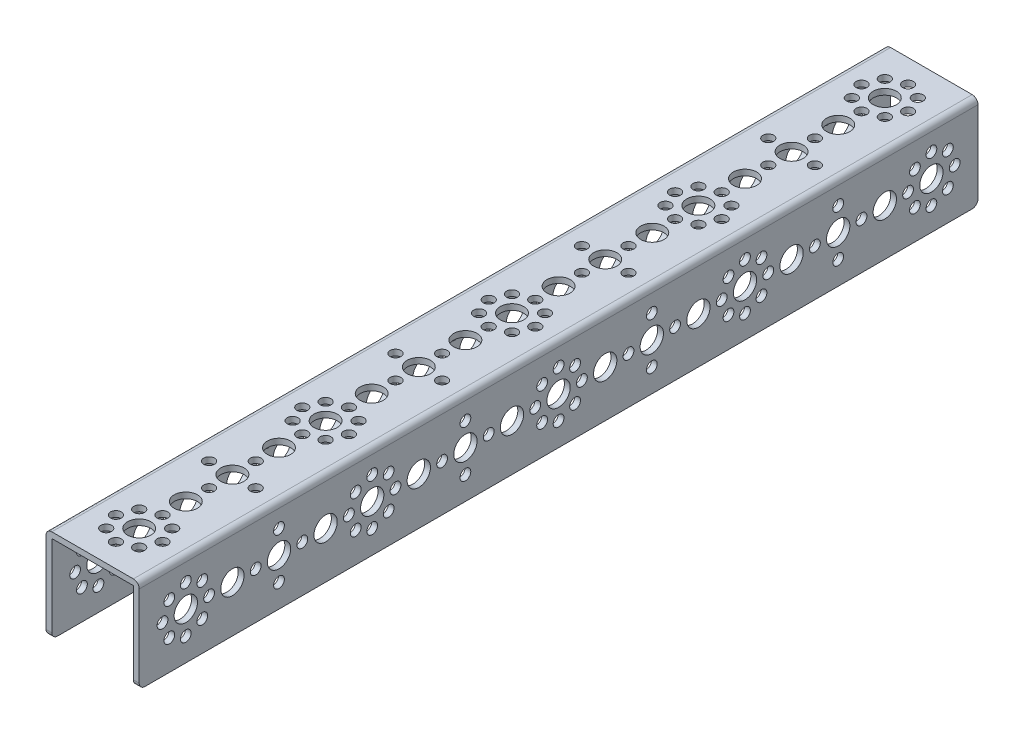
SolidWorks part; units mm, degrees
ref_plane "Front Plane" through (0, 0, 0) normal (0, 0, 1) x (1, 0, 0)
ref_plane "Top Plane" through (0, 0, 0) normal (0, 1, 0) x (1, 0, 0)
ref_plane "Right Plane" through (0, 0, 0) normal (1, 0, 0) x (0, 0, -1)
sketch "Sketch1" plane through (0, 0, 0) normal (0, 0, 1) x (1, 0, 0)
  line L0 (14, -16) -> (16, -16)
  line L1 (-16, 16) -> (16, 16)
  line L2 (-16, 16) -> (-16, -16)
  line L3 (-16, -16) -> (-14, -16)
  line L4 (16, 16) -> (16, -16)
  line L5 (-16, 16) -> (16, -16) construction
  line L6 (-16, -16) -> (16, 16) construction
  line L7 (-14, 14) -> (14, 14)
  line L8 (-14, 14) -> (-14, -16)
  line L10 (14, 14) -> (14, -16)
  point P0 (0, 0)
  dimension "D1" = 32
  dimension "D2" = 32
  dimension "D3" = 2
  dimension "D4" = 2
extrude "Boss-Extrude1" add sketch "Sketch1" against normal blind 288
sketch "Sketch2" plane through (0, 16, 0) normal (0, 1, 0) x (1, 0, 0)
  line L0 (0, 0) -> (0, 307.3895) construction
  line L1 (16, 0) -> (-16, 0) construction
  line L2 (-26.7249, 144) -> (42.2171, 144) construction
  circle B0 centre (0, 256) radius 4
  circle B1 centre (0, 224) radius 4
  circle B2 centre (0.1754, 192) radius 4
  circle B3 centre (0, 160) radius 4
  circle B4 centre (0, 240) radius 4
  circle B5 centre (0, 232) radius 1.85
  circle B6 centre (0, 248) radius 1.85
  circle B7 centre (-8, 240) radius 1.85
  circle B8 centre (8, 240) radius 1.85
  circle B9 centre (0, 264) radius 1.85
  circle B10 centre (-8, 272) radius 1.85
  circle B11 centre (0, 272) radius 4
  circle B12 centre (8, 272) radius 1.85
  circle B13 centre (5.66, 277.66) radius 1.85
  circle B14 centre (-5.66, 277.66) radius 1.85
  circle B15 centre (0, 280) radius 1.85
  circle B16 centre (5.66, 266.34) radius 1.85
  circle B17 centre (-5.66, 266.34) radius 1.85
  circle B18 centre (0, 176) radius 4
  circle B19 centre (0, 168) radius 1.85
  circle B20 centre (0, 184) radius 1.85
  circle B21 centre (-8, 176) radius 1.85
  circle B22 centre (8, 176) radius 1.85
  circle B23 centre (0, 200) radius 1.85
  circle B24 centre (-8, 208) radius 1.85
  circle B25 centre (0, 208) radius 4
  circle B26 centre (8, 208) radius 1.85
  circle B27 centre (5.66, 213.66) radius 1.85
  circle B28 centre (-5.66, 213.66) radius 1.85
  circle B29 centre (0, 216) radius 1.85
  circle B30 centre (5.66, 202.34) radius 1.85
  circle B31 centre (-5.66, 202.34) radius 1.85
  circle B32 centre (0, 32) radius 4
  circle B33 centre (0, 64) radius 4
  circle B34 centre (-0.1754, 96) radius 4
  circle B35 centre (0, 128) radius 4
  circle B36 centre (0, 48) radius 4
  circle B37 centre (0, 56) radius 1.85
  circle B38 centre (0, 40) radius 1.85
  circle B39 centre (8, 48) radius 1.85
  circle B40 centre (-8, 48) radius 1.85
  circle B41 centre (0, 24) radius 1.85
  circle B42 centre (8, 16) radius 1.85
  circle B43 centre (0, 16) radius 4
  circle B44 centre (-8, 16) radius 1.85
  circle B45 centre (-5.66, 10.34) radius 1.85
  circle B46 centre (5.66, 10.34) radius 1.85
  circle B47 centre (0, 8) radius 1.85
  circle B48 centre (-5.66, 21.66) radius 1.85
  circle B49 centre (5.66, 21.66) radius 1.85
  circle B50 centre (0, 112) radius 4
  circle B51 centre (0, 120) radius 1.85
  circle B52 centre (0, 104) radius 1.85
  circle B53 centre (8, 112) radius 1.85
  circle B54 centre (-8, 112) radius 1.85
  circle B55 centre (0, 88) radius 1.85
  circle B56 centre (8, 80) radius 1.85
  circle B57 centre (0, 80) radius 4
  circle B58 centre (-8, 80) radius 1.85
  circle B59 centre (-5.66, 74.34) radius 1.85
  circle B60 centre (5.66, 74.34) radius 1.85
  circle B61 centre (0, 72) radius 1.85
  circle B62 centre (-5.66, 85.66) radius 1.85
  circle B63 centre (5.66, 85.66) radius 1.85
  circle B64 centre (0, 136) radius 1.85
  circle B65 centre (-8, 144) radius 1.85
  circle B66 centre (0, 144) radius 4
  circle B67 centre (8, 144) radius 1.85
  circle B68 centre (5.66, 149.66) radius 1.85
  circle B69 centre (-5.66, 149.66) radius 1.85
  circle B70 centre (0, 152) radius 1.85
  circle B71 centre (5.66, 138.34) radius 1.85
  circle B72 centre (-5.66, 138.34) radius 1.85
sketch_block_instance "TETRIX 288 Pattern-3"
sketch_block "TETRIX 288 Pattern" parameters "D1"=16, "D2"=16, "D3"=16, "D4"=16, "D5"=16, "D6"=16, "D7"=16, "D8"=16, "D9"=16, "D10"=16, "D11"=16, "D12"=16, "D13"=16, "D14"=16, "D15"=16
extrude "Cut-Extrude1" cut sketch "Sketch2" against normal through all
sketch "Sketch3" plane through (16, 0, 0) normal (1, 0, 0) x (0, 0, -1)
  line L0 (-3.4954, 0) -> (176.3323, 0) construction
  line L1 (144, 24.5569) -> (144, -31.5997) construction
  circle B0 centre (32, 0) radius 4
  circle B1 centre (64, 0) radius 4
  circle B2 centre (96, 0.1754) radius 4
  circle B3 centre (128, 0) radius 4
  circle B4 centre (48, 0) radius 4
  circle B5 centre (56, 0) radius 1.85
  circle B6 centre (40, 0) radius 1.85
  circle B7 centre (48, -8) radius 1.85
  circle B8 centre (48, 8) radius 1.85
  circle B9 centre (24, 0) radius 1.85
  circle B10 centre (16, -8) radius 1.85
  circle B11 centre (16, 0) radius 4
  circle B12 centre (16, 8) radius 1.85
  circle B13 centre (10.34, 5.66) radius 1.85
  circle B14 centre (10.34, -5.66) radius 1.85
  circle B15 centre (8, 0) radius 1.85
  circle B16 centre (21.66, 5.66) radius 1.85
  circle B17 centre (21.66, -5.66) radius 1.85
  circle B18 centre (112, 0) radius 4
  circle B19 centre (120, 0) radius 1.85
  circle B20 centre (104, 0) radius 1.85
  circle B21 centre (112, -8) radius 1.85
  circle B22 centre (112, 8) radius 1.85
  circle B23 centre (88, 0) radius 1.85
  circle B24 centre (80, -8) radius 1.85
  circle B25 centre (80, 0) radius 4
  circle B26 centre (80, 8) radius 1.85
  circle B27 centre (74.34, 5.66) radius 1.85
  circle B28 centre (74.34, -5.66) radius 1.85
  circle B29 centre (72, 0) radius 1.85
  circle B30 centre (85.66, 5.66) radius 1.85
  circle B31 centre (85.66, -5.66) radius 1.85
  circle B32 centre (256, 0) radius 4
  circle B33 centre (224, 0) radius 4
  circle B34 centre (192, -0.1754) radius 4
  circle B35 centre (160, 0) radius 4
  circle B36 centre (240, 0) radius 4
  circle B37 centre (232, 0) radius 1.85
  circle B38 centre (248, 0) radius 1.85
  circle B39 centre (240, 8) radius 1.85
  circle B40 centre (240, -8) radius 1.85
  circle B41 centre (264, 0) radius 1.85
  circle B42 centre (272, 8) radius 1.85
  circle B43 centre (272, 0) radius 4
  circle B44 centre (272, -8) radius 1.85
  circle B45 centre (277.66, -5.66) radius 1.85
  circle B46 centre (277.66, 5.66) radius 1.85
  circle B47 centre (280, 0) radius 1.85
  circle B48 centre (266.34, -5.66) radius 1.85
  circle B49 centre (266.34, 5.66) radius 1.85
  circle B50 centre (176, 0) radius 4
  circle B51 centre (168, 0) radius 1.85
  circle B52 centre (184, 0) radius 1.85
  circle B53 centre (176, 8) radius 1.85
  circle B54 centre (176, -8) radius 1.85
  circle B55 centre (200, 0) radius 1.85
  circle B56 centre (208, 8) radius 1.85
  circle B57 centre (208, 0) radius 4
  circle B58 centre (208, -8) radius 1.85
  circle B59 centre (213.66, -5.66) radius 1.85
  circle B60 centre (213.66, 5.66) radius 1.85
  circle B61 centre (216, 0) radius 1.85
  circle B62 centre (202.34, -5.66) radius 1.85
  circle B63 centre (202.34, 5.66) radius 1.85
  circle B64 centre (152, 0) radius 1.85
  circle B65 centre (144, -8) radius 1.85
  circle B66 centre (144, 0) radius 4
  circle B67 centre (144, 8) radius 1.85
  circle B68 centre (138.34, 5.66) radius 1.85
  circle B69 centre (138.34, -5.66) radius 1.85
  circle B70 centre (136, 0) radius 1.85
  circle B71 centre (149.66, 5.66) radius 1.85
  circle B72 centre (149.66, -5.66) radius 1.85
sketch_block_instance "TETRIX 288 Pattern-5"
extrude "Cut-Extrude2" cut sketch "Sketch3" against normal through all
fillet "Fillet1" radius 2 6 edges at (-15, -16, -288) (15, -16, -288) (-15, -16, 0) (15, -16, 0) (-16, 16, -144) (16, 16, -144)
